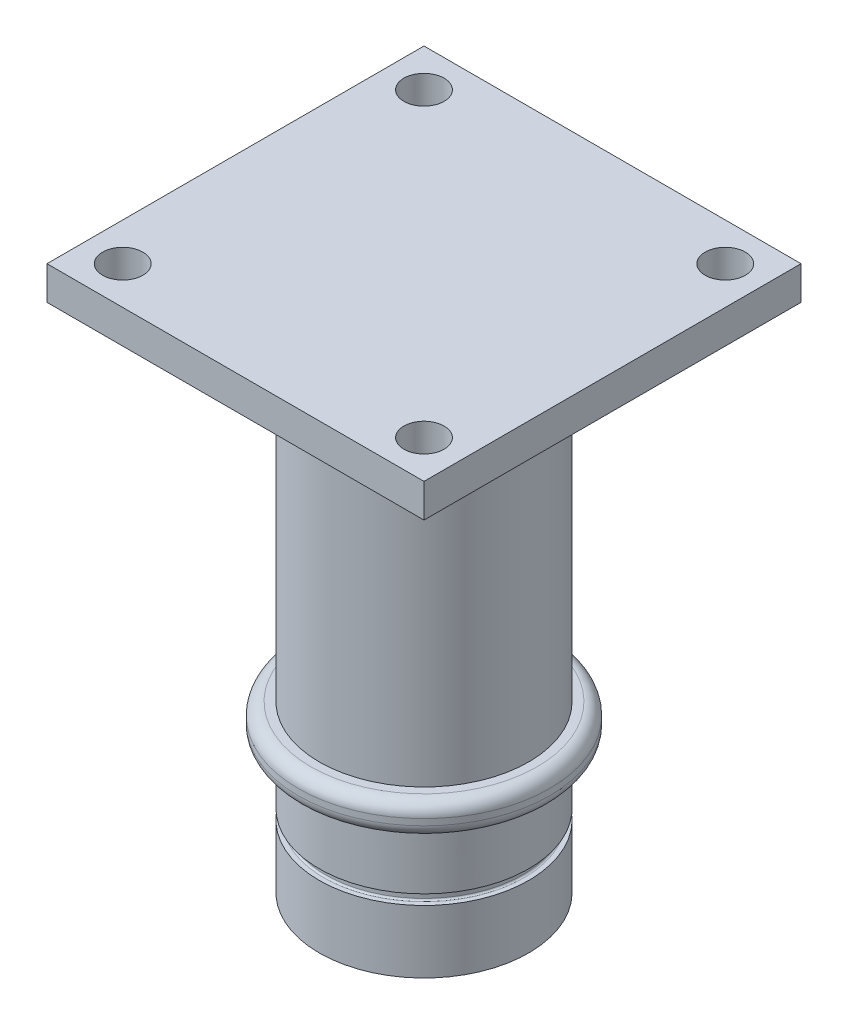
SolidWorks part; units mm, degrees
ref_plane "Front Plane" through (0, 0, 0) normal (0, 0, 1) x (1, 0, 0)
ref_plane "Top Plane" through (0, 0, 0) normal (0, 1, 0) x (1, 0, 0)
ref_plane "Right Plane" through (0, 0, 0) normal (1, 0, 0) x (0, 0, -1)
sketch "Sketch1" plane through (0, 0, 0) normal (0, 1, 0) x (1, 0, 0)
  circle A0 centre (0, 0) radius 12.5
  dimension "D1" = 25
extrude "Boss-Extrude1" add sketch "Sketch1" along normal blind 16
sketch "Sketch3" plane through (0, 0, 0) normal (0, -1, 0) x (-1, 0, 0)
  text T0 "<b>25mm</b>"
extrude "Boss-Extrude2" add sketch "Sketch3" along normal blind 0.32
sketch "Sketch4" plane through (0, 16, 0) normal (0, 1, 0) x (1, 0, 0)
  circle A0 centre (0, 0) radius 15
  dimension "D1" = 30
extrude "Boss-Extrude3" add sketch "Sketch4" along normal blind 45
sketch "Sketch5" plane through (0, 61, 0) normal (0, 1, 0) x (1, 0, 0)
  line L1 (-22.5, 22.5) -> (22.5, 22.5)
  line L2 (-22.5, 22.5) -> (-22.5, -22.5)
  line L3 (-22.5, -22.5) -> (22.5, -22.5)
  line L4 (22.5, 22.5) -> (22.5, -22.5)
  line L5 (-22.5, 22.5) -> (22.5, -22.5) construction
  line L6 (-22.5, -22.5) -> (22.5, 22.5) construction
  point P0 (0, 0)
  dimension "D1" = 45
  dimension "D2" = 45
extrude "Boss-Extrude4" add sketch "Sketch5" along normal blind 4
fillet "Fillet1" radius 1.5 1 edges at (0, 16, 15)
hole_wizard "M4 Clearance Hole1" positions "Sketch6" profile "Sketch8" hole size "M4" standard "ANSI Metric" end condition through all
sketch "Sketch6" plane through (0, 61, 0) normal (0, -1, 0) x (-1, 0, 0)
  line L0 (22.5, 22.5) -> (-22.5, -22.5) construction
  line L1 (22.5, 22.5) -> (22.5, -22.5) construction
  line L2 (-22.5, 22.5) -> (22.5, 22.5) construction
  line L4 (-22.5, 22.5) -> (22.5, -22.5) construction
  point P0 (-17.978, 17.978)
  point P2 (17.978, 17.978)
  point P4 (17.978, -17.978)
  point P6 (-17.978, -17.978)
sketch "Sketch8" plane through (17.978, 61, -17.978) normal (1, 0, 0) x (0, 0, -1)
  line L0 (0, 0) -> (0, 4)
  line L1 (0, 4) -> (2.4, 4)
  line L2 (2.4, 4) -> (2.4, 0)
  line L5 (2.4, 0) -> (0, 0)
  line L11 (0, -6.35) -> (0, 107.95) construction
  dimension "Thru Hole Dia." = 4.8
  dimension "Thru Hole Depth" = 4
ref_plane "Plane1" through (0, 12, 0) normal (-1, 0, 0) x (0, 0, -1)
ref_plane "Plane2" through (0, 12, 0) normal (-1, 0, 0) x (0, 0, -1)
ref_plane "Plane3" through (0, 12, 0) normal (-1, 0, 0) x (0, 0, -1)
ref_plane "Plane4" through (0, 12, 0) normal (-1, 0, 0) x (0, 0, -1)
ref_plane "Plane5" through (0, 12, 0) normal (-1, 0, 0) x (0, 0, -1)
ref_plane "Plane6" through (0, 12, 0) normal (-1, 0, 0) x (0, 0, -1)
ref_plane "Plane7" through (0, 12, 0) normal (-1, 0, 0) x (0, 0, -1)
ref_plane "Plane8" through (0, 12, 0) normal (-1, 0, 0) x (0, 0, -1)
sketch "Sketch24" plane through (0, 12, 0) normal (-1, 0, 0) x (0, 0, -1)
  line L0 (11.95, 3.3) -> (15.15, 3.3)
  line L1 (15.15, 3.3) -> (15.15, 4.5)
  line L2 (15.15, 4.5) -> (11.95, 4.5)
  line L3 (11.75, 4.3) -> (11.75, 3.5)
  line L4 (0, -50) -> (0, 50) construction
  line L5 (13.5, -4) -> (-13.5, -4) construction
  line L6 (13.5, -4) -> (-13.5, -4) construction
  arc A0 (11.75, 3.5) -> (11.95, 3.3) centre (11.95, 3.5) ccw
  arc A1 (11.75, 4.3) -> (11.95, 4.5) centre (11.95, 4.3) cw
  dimension "D1" = 0.2
  dimension "D2" = 0.2
  dimension "D3" = 7.3
  dimension "D4" = 11.75
  dimension "D5" = 15.15
  dimension "D6" = 1.2
revolve "Groove for ANSI B27.7 - 3AM1-25, Basic External Retaining Ring1" cut sketch "Sketch24"
ref_axis "Axis1" through (0, 61, 0) along (0, -1, 0)
sketch "Sketch26" plane through (0, 0, 0) normal (1, 0, 0) x (0, 0, -1)
  line L0 (12.5, 59.7644) -> (15.9702, 59.7644)
  line L2 (15.9702, 59.7644) -> (15.9702, 19.745)
  line L3 (15.9702, 19.745) -> (12.5, 19.745)
  line L5 (12.5, 19.745) -> (12.5, 59.7644)
revolve "Cut-Revolve1" cut sketch "Sketch26" angle 360 about axis through (0, 61, 0) along (0, -1, 0)
fillet "Fillet3" radius 1.5 1 edges at (0, 19.745, 15)
